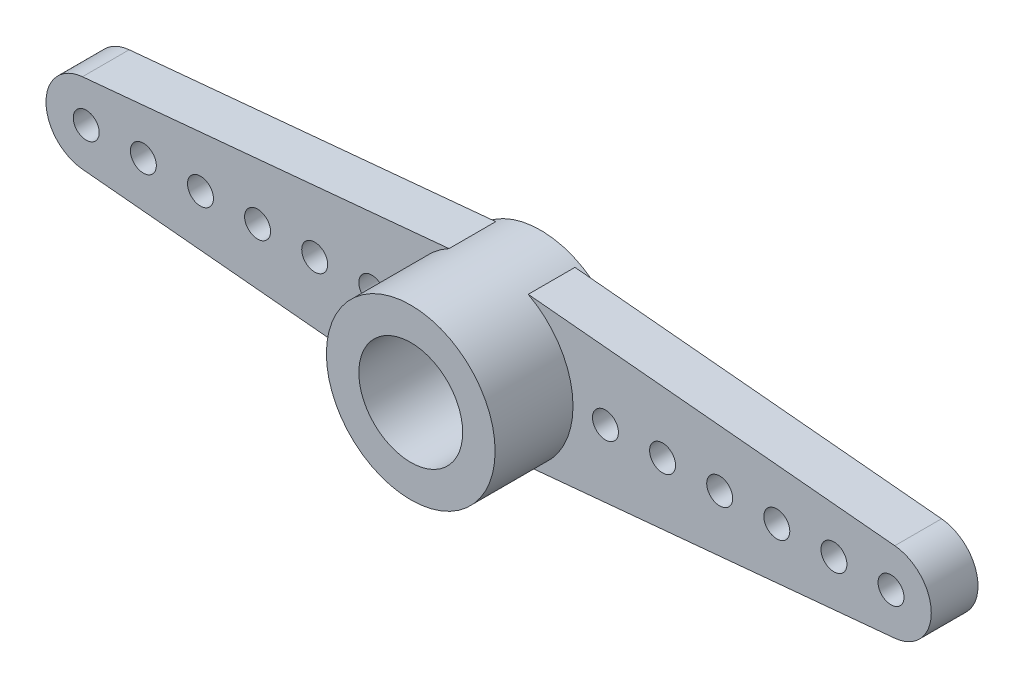
SolidWorks part; units mm, degrees
ref_plane "Ön Düzlem" through (0, 0, 0) normal (0, 0, 1) x (1, 0, 0)
ref_plane "Üst Düzlem" through (0, 0, 0) normal (0, 1, 0) x (1, 0, 0)
ref_plane "Sağ Düzlem" through (0, 0, 0) normal (1, 0, 0) x (0, 0, -1)
sketch "Sketch1" plane through (0, 0, 0) normal (0, 0, 1) x (1, 0, 0)
  line L0 (1.5252, 2.8699) -> (15.645, 1.5432)
  line L1 (0, 0) -> (0, 4.8627) construction
  line L2 (0, 0) -> (0, -5.6571) construction
  line L3 (-18.8826, 0) -> (18.8826, 0) construction
  line L4 (1.5252, -2.8699) -> (15.645, -1.5432)
  line L7 (-1.5252, -2.8699) -> (-15.645, -1.5432)
  line L8 (-1.5252, 2.8699) -> (-15.645, 1.5432)
  arc A0 (-1.5252, -2.8699) -> (1.5252, -2.8699) centre (0, 0) ccw
  arc A1 (15.645, -1.5432) -> (15.645, 1.5432) centre (15.5, 0) ccw
  arc A3 (-15.645, -1.5432) -> (-15.645, 1.5432) centre (-15.5, 0) cw
  arc A4 (1.5252, 2.8699) -> (-1.5252, 2.8699) centre (0, 0) ccw
  dimension "D2" = 3.1
  dimension "D3" = 6.5
  dimension "D1" = 15.5
extrude "Boss-Extrude1" add sketch "Sketch1" along normal blind 1.8
sketch "Sketch2" plane through (0, 0, 0) normal (0, 0, -1) x (-1, 0, 0)
  circle A0 centre (0, 0) radius 3.25
  circle A1 centre (0, 0) radius 2.5
extrude "Boss-Extrude3" add sketch "Sketch2" along normal blind 0.2 contours A1 | A0
sketch "Sketch4" plane through (0, 0, 1.8) normal (0, 0, 1) x (1, 0, 0)
  circle A0 centre (0, 0) radius 3.25
  circle A1 centre (0, 0) radius 2
  dimension "D1" = 6.5
extrude "Boss-Extrude4" add sketch "Sketch4" along normal blind 3
sketch "Sketch5" plane through (0, 0, 1.8) normal (0, 0, 1) x (1, 0, 0)
  circle A0 centre (0, 0) radius 1.5
extrude "Cut-Extrude1" cut sketch "Sketch5" against normal up to next
sketch "Sketch6" plane through (0, 0, 0) normal (0, 0, -1) x (-1, 0, 0)
  circle A0 centre (15.5, 0) radius 0.5
  circle A1 centre (13.3, 0) radius 0.5
  circle A2 centre (11.1, 0) radius 0.5
  circle A3 centre (8.9, 0) radius 0.5
  circle A4 centre (6.7, 0) radius 0.5
  circle A5 centre (4.5, 0) radius 0.5
  circle A6 centre (-4.5, 0) radius 0.5
  circle A7 centre (-6.7, 0) radius 0.5
  circle A8 centre (-8.9, 0) radius 0.5
  circle A9 centre (-11.1, 0) radius 0.5
  circle A10 centre (-13.3, 0) radius 0.5
  circle A11 centre (-15.5, 0) radius 0.5
  point P3 (0, 0)
  dimension "D3" = 6
extrude "Cut-Extrude2" cut sketch "Sketch6" against normal up to next
